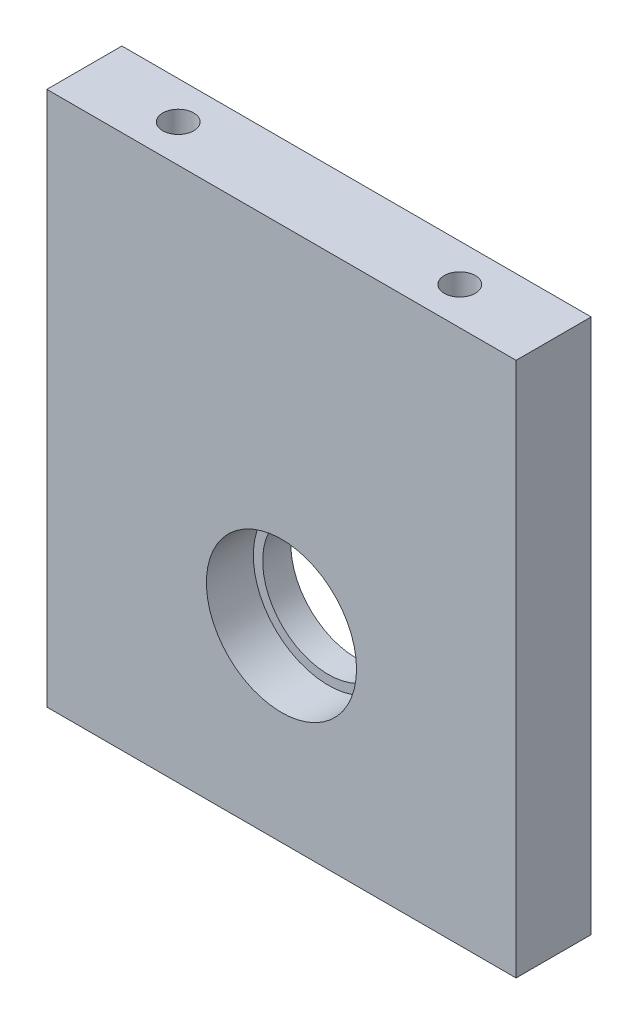
SolidWorks part; units mm, degrees
ref_plane "Front" through (0, 0, 0) normal (0, 0, 1) x (1, 0, 0)
ref_plane "Top" through (0, 0, 0) normal (0, 1, 0) x (1, 0, 0)
ref_plane "Right" through (0, 0, 0) normal (1, 0, 0) x (0, 0, -1)
sketch "Esquisse1" plane through (0, 0, 0) normal (0, 0, 1) x (1, 0, 0)
  line L0 (25, 0) -> (25, 20) construction
  line L1 (0, 0) -> (50, 0)
  line L2 (0, 0) -> (0, 57)
  line L3 (0, 57) -> (50, 57)
  line L4 (50, 0) -> (50, 57)
  circle A0 centre (25, 20) radius 7
  dimension "D1" = 20
  dimension "D2" = 14
  dimension "D3" = 50
  dimension "D4" = 57
extrude "Boss.-Extru.1" add sketch "Esquisse1" along normal blind 8
sketch "Esquisse2" plane through (0, 0, 8) normal (0, 0, 1) x (1, 0, 0)
  circle A0 centre (25, 20) radius 8
  dimension "D1" = 16
extrude "Enlèv. mat.-Extru.1" cut sketch "Esquisse2" against normal blind 5
sketch "Esquisse3" plane through (0, 57, 0) normal (0, 1, 0) x (1, 0, 0)
  line L0 (0, -4) -> (50, -4) construction
  line L1 (0, -8) -> (0, 0) construction
  line L2 (50, -8) -> (50, 0) construction
  line L3 (25, -4) -> (25, 0) construction
  line L4 (50, 0) -> (0, 0) construction
  circle A0 centre (10, -4) radius 1.65
  circle A1 centre (40, -4) radius 1.65
  dimension "D1" = 3.3
  dimension "D2" = 30
extrude "Enlèv. mat.-Extru.2" cut sketch "Esquisse3" against normal blind 10
